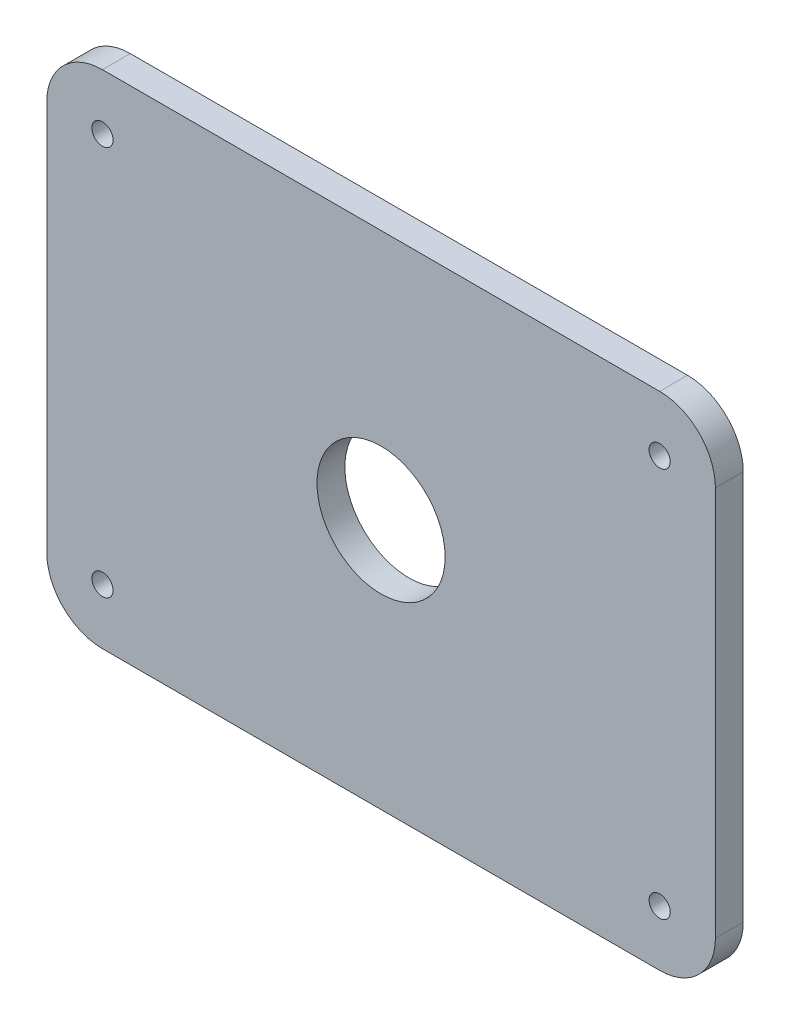
SolidWorks part; units mm, degrees
ref_plane "Front Plane" through (0, 0, 0) normal (0, 0, 1) x (1, 0, 0)
ref_plane "Top Plane" through (0, 0, 0) normal (0, 1, 0) x (1, 0, 0)
ref_plane "Right Plane" through (0, 0, 0) normal (1, 0, 0) x (0, 0, -1)
sketch "Sketch3" plane through (0, 0, 0) normal (0, 0, 1) x (1, 0, 0)
  line L1 (-50, 45) -> (50, 45)
  line L2 (-60, 35) -> (-60, -35)
  line L3 (-50, -45) -> (50, -45)
  line L4 (60, 35) -> (60, -35)
  line L5 (-60, 45) -> (60, -45) construction
  line L6 (-60, -45) -> (60, 45) construction
  arc A0 (-60, -35) -> (-50, -45) centre (-50, -35) ccw
  arc A1 (50, -45) -> (60, -35) centre (50, -35) ccw
  arc A2 (60, 35) -> (50, 45) centre (50, 35) ccw
  arc A3 (-50, 45) -> (-60, 35) centre (-50, 35) ccw
  circle A4 centre (-50, 35) radius 1.9
  circle A5 centre (50, 35) radius 1.9
  circle A6 centre (50, -35) radius 1.9
  circle A7 centre (-50, -35) radius 1.9
  circle A8 centre (0, 0) radius 11.5
  point P0 (0, 0)
  dimension "D3" = 10
  dimension "D1" = 120
  dimension "D2" = 90
extrude "Boss-Extrude2" add sketch "Sketch3" along normal blind 5
